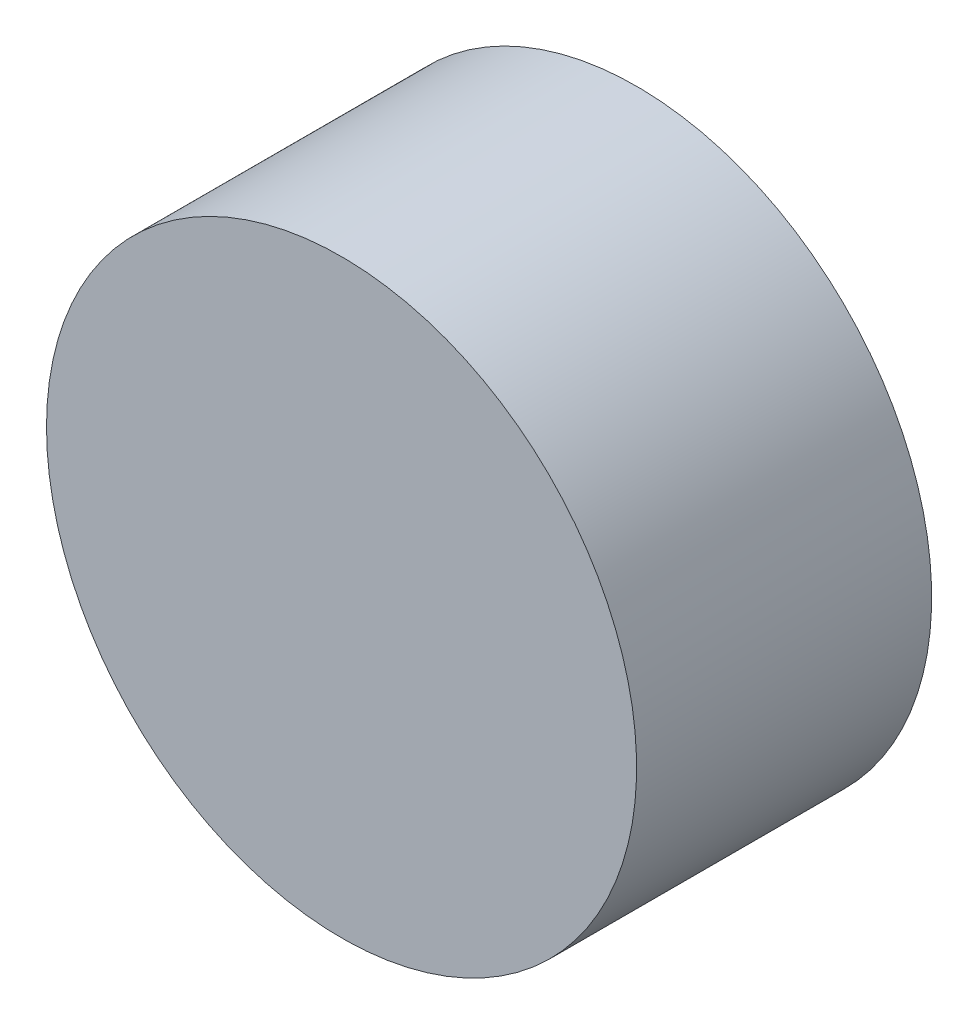
SolidWorks part; units mm, degrees
material "PE Low Density Film"
ref_plane "Front Plane" through (0, 0, 0) normal (0, 0, 1) x (1, 0, 0)
ref_plane "Top Plane" through (0, 0, 0) normal (0, 1, 0) x (1, 0, 0)
ref_plane "Right Plane" through (0, 0, 0) normal (1, 0, 0) x (0, 0, -1)
ref_plane "Plane1" through (0, 0, 0) normal (0, -1, 0) x (-1, 0, 0)
sketch "Sketch3" plane through (0, 0, 0) normal (0, -1, 0) x (-1, 0, 0)
  line L0 (0, 0) -> (0, -44.7518) construction
  line L1 (25.4, -25.4) -> (25.4, 0) construction
  line L2 (25.4, -25.4) -> (25.4, 0)
  line L3 (28.575, -25.4) -> (28.575, 0)
  line L4 (28.575, -25.4) -> (28.575, -28.575)
  line L5 (28.575, -28.575) -> (0, -28.575)
  line L6 (-25.4, -25.4) -> (25.4, -25.4) construction
  line L7 (0, -25.4) -> (25.4, -25.4)
  line L8 (0, -28.575) -> (0, -25.4)
  line L9 (28.575, 0) -> (25.4, 0)
  dimension "D2" = 3.175
  dimension "D1" = 3.175
revolve "Revolve1" add sketch "Sketch3" angle 360 about L0
